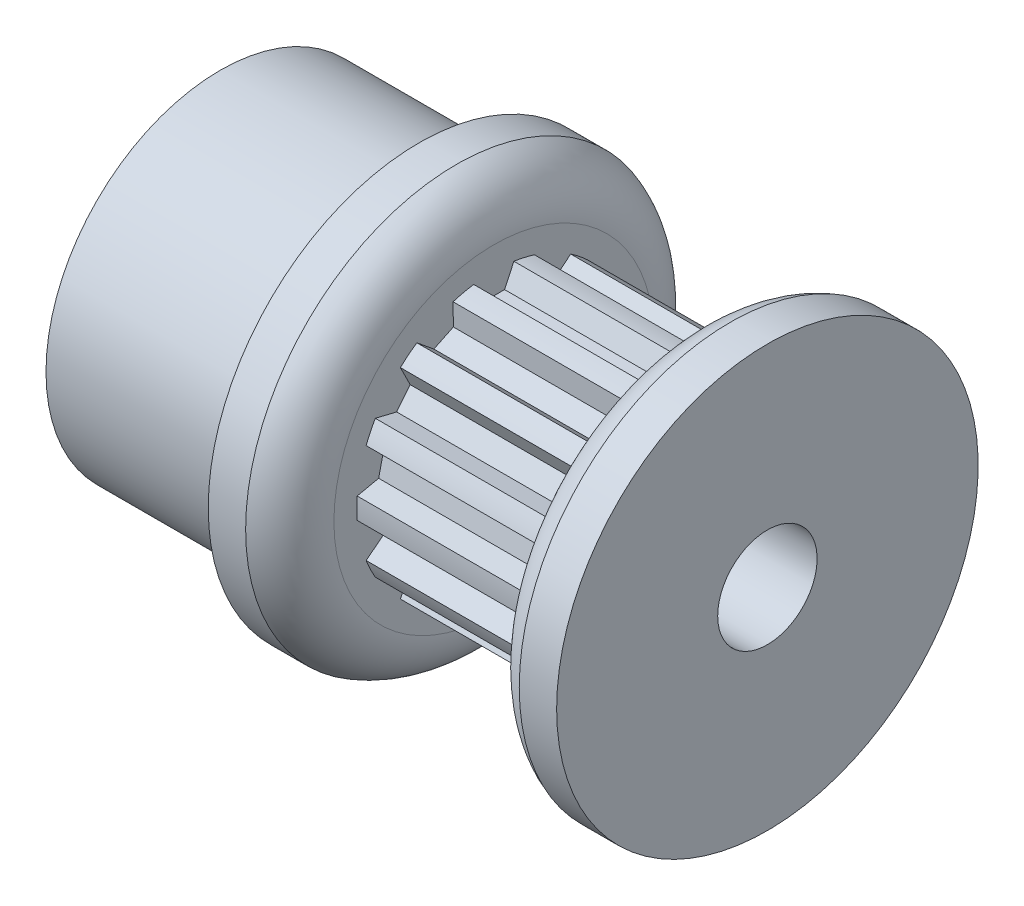
SolidWorks part; units mm, degrees
ref_plane "Front Plane" through (0, 0, 0) normal (0, 0, 1) x (1, 0, 0)
ref_plane "Top Plane" through (0, 0, 0) normal (0, 1, 0) x (1, 0, 0)
ref_plane "Right Plane" through (0, 0, 0) normal (1, 0, 0) x (0, 0, -1)
sketch "Sketch2" plane through (0, 0, 0) normal (1, 0, 0) x (0, 0, -1)
  line L3 (0, 0) -> (0, 3.7084) construction
  line L6 (0, -4.2164) -> (0, -4.5339) construction
  line L7 (-0.5715, 4.1775) -> (-0.3452, 3.6923)
  line L8 (0.5715, 4.1775) -> (0.3452, 3.6923)
  line L9 (-0.5715, 4.1775) -> (-0.6416, 4.3278)
  line L10 (0.5715, 4.1775) -> (0.6416, 4.3278)
  line L12 (-0.3452, 3.6923) -> (0.3452, 3.6923)
  line L14 (0, 4.2164) -> (0, 4.5339) construction
  line L15 (0, 0) -> (0, -1.143) construction
  circle A0 centre (0, 0) radius 4.5339 construction
  circle A1 centre (0, 0) radius 3.7084 construction
  circle A2 centre (0, 0) radius 4.2164 construction
  arc A7 (0.6416, 4.3278) -> (-0.6416, 4.3278) centre (0, 0) ccw
  point P5 (0, 4.3751)
  dimension "D3" = 0.3175
  dimension "D1" = 50
sketch "Sketch1" plane through (0, 0, 0) normal (0, 0, 1) x (1, 0, 0)
  line L0 (-8.7376, 0) -> (8.7376, 0) construction
  line L1 (-8.7376, 1.5875) -> (8.7376, 1.5875)
  line L2 (-8.7376, 1.5875) -> (-8.7376, 5.5626)
  line L3 (-2.3876, 6.731) -> (-1.1938, 6.731)
  line L4 (0, 4.5339) -> (0, 5.1054)
  line L5 (0, 5.6769) -> (0, 4.5339) construction
  line L6 (0, 4.5339) -> (6.35, 4.5339)
  line L7 (6.35, 4.5339) -> (6.35, 5.1054)
  line L8 (6.35, 4.5339) -> (8.7376, 4.5339) construction
  line L9 (7.5438, 6.731) -> (8.7376, 6.731)
  line L10 (8.7376, 6.731) -> (8.7376, 1.5875)
  line L11 (7.5438, 4.5339) -> (7.5438, 6.731) construction
  line L12 (-5.5626, 5.5626) -> (-5.5626, 1.5875) construction
  line L13 (-2.3876, 6.731) -> (-2.3876, 5.5626)
  line L14 (-2.3876, 5.5626) -> (-8.7376, 5.5626)
  arc A0 (6.35, 5.1054) -> (7.5438, 6.731) centre (8.0537, 5.1054) cw
  arc A1 (0, 5.1054) -> (-1.1938, 6.731) centre (-1.7037, 5.1054) ccw
  dimension "Bore Size" = 3.175
  dimension "Overall Width" = 17.4752
  dimension "Inside Width" = 6.35
  dimension "OD" = 13.462
  dimension "D2" = 9.0678
  dimension "D3" = 1.143
  dimension "D4" = 0.5715
  dimension "Outside Width" = 11.1252
revolve "Revolve1" add sketch "Sketch1" angle 360 mid plane about L0
sketch "Sketch4" plane through (0, 0, 0) normal (1, 0, 0) x (0, 0, -1)
  circle A0 centre (0, 0) radius 4.3751
  circle A2 centre (0, 0) radius 4.5339
  circle A3 centre (0, 0) radius 4.5339 construction
extrude "Cut-Extrude2" cut sketch "Sketch4" along normal up to surface (6.35 mm away) up to face at (6.35, 0, 4.5339)
sketch "Sketch3" plane through (0, 0, 0) normal (1, 0, 0) x (0, 0, -1)
  line L2 (-0.5715, 4.1775) -> (-0.3452, 3.6923) construction
  line L3 (-0.3452, 3.6923) -> (0.3452, 3.6923) construction
  line L4 (0.5715, 4.1775) -> (0.3452, 3.6923) construction
  line L5 (-0.6416, 4.3278) -> (-0.3452, 3.6923)
  line L6 (-0.3452, 3.6923) -> (0.3452, 3.6923)
  line L7 (0.6416, 4.3278) -> (0.3452, 3.6923)
  arc A1 (0.6416, 4.3278) -> (-0.6416, 4.3278) centre (0, 0) ccw construction
  arc A2 (0.6416, 4.3278) -> (-0.6416, 4.3278) centre (0, 0) ccw
extrude "Cut-Extrude1" cut sketch "Sketch3" along normal up to surface (6.35 mm away) up to face at (6.35, 0, 5.1054)
pattern_circular "CirPattern1" count 14 over 360 about axis through (0, 0, 0) along (1, 0, 0) of "Cut-Extrude1"
sketch "Sketch5" plane through (0, 0, 0) normal (0, 0, 1) x (1, 0, 0)
  line L1 (6.35, 5.1054) -> (6.35, -5.1054) construction
  point P0 (6.35, 0)
equation "\"D3@Sketch2\" = (\"hs@Sketch2\"-\"ht@Sketch2\")/2"
equation "\"D2@Sketch1\" = \"PD@Sketch2\""
equation "\"D3@Sketch1\" = \"hs@Sketch2\""
equation "\"D4@Sketch1\" = \"D3@Sketch1\"/2"
